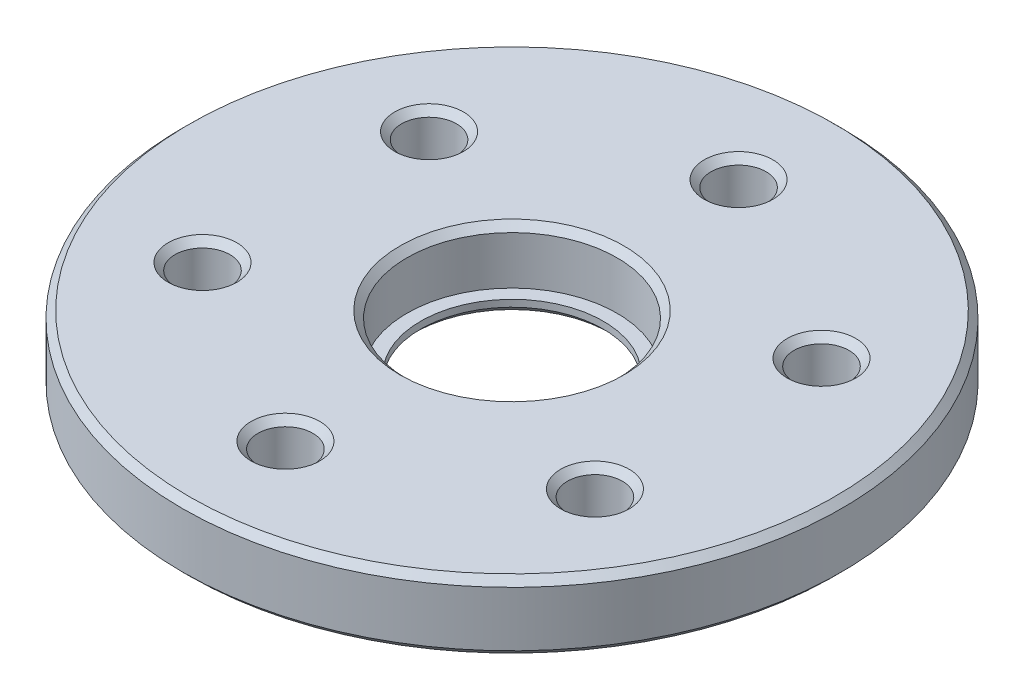
SolidWorks part; units mm, degrees
ref_plane "Front Plane" through (0, 0, 0) normal (0, 0, 1) x (1, 0, 0)
ref_plane "Top Plane" through (0, 0, 0) normal (0, 1, 0) x (1, 0, 0)
ref_plane "Right Plane" through (0, 0, 0) normal (1, 0, 0) x (0, 0, -1)
sketch "Sketch1" plane through (0, 0, 0) normal (0, 1, 0) x (1, 0, 0)
  circle A0 centre (0, 0) radius 24
  circle A1 centre (0, 0) radius 7.65
  dimension "D1" = 48
  dimension "D2" = 15.3
extrude "Boss-Extrude1" add sketch "Sketch1" along normal blind 4
sketch "Sketch2" plane through (0, 4, 0) normal (0, 1, 0) x (1, 0, 0)
  circle A0 centre (0, 16.5) radius 2
  dimension "D1" = 16.5
  dimension "D2" = 4
extrude "Cut-Extrude1" cut sketch "Sketch2" against normal through all
pattern_circular "CirPattern2" count 6 over 360 about axis through (0, 0, 0) along (0, 1, 0) of "Cut-Extrude1"
sketch "Sketch3" plane through (0, 0, 0) normal (0, 1, 0) x (1, 0, 0)
  circle A0 centre (-14.2894, -8.25) radius 2 construction
  circle A1 centre (0, -16.5) radius 2 construction
  circle A2 centre (14.2894, -8.25) radius 2 construction
  circle A3 centre (14.2894, 8.25) radius 2 construction
  circle A4 centre (0, 0) radius 24
  circle A5 centre (0, 16.5) radius 2 construction
  circle A6 centre (-14.2894, 8.25) radius 2 construction
  circle A7 centre (0, 0) radius 6.65
  circle A8 centre (-14.2894, -8.25) radius 2
  circle A9 centre (0, -16.5) radius 2
  circle A10 centre (14.2894, -8.25) radius 2
  circle A11 centre (14.2894, 8.25) radius 2
  circle A13 centre (0, 16.5) radius 2
  circle A14 centre (-14.2894, 8.25) radius 2
  circle A19 centre (0, 0) radius 24 construction
  circle A20 centre (0, 0) radius 7.65 construction
  dimension "D1" = 0
  dimension "D2" = 1
extrude "Boss-Extrude2" add sketch "Sketch3" against normal blind 1
chamfer "Chamfer1" distance 0.5 angle 45 16 edges at (0, 4, 7.65) (0, 4, 24) (0, 4, -14.5) (-12.5574, 4, -7.25) (-12.5574, 4, 7.25) (0, 4, 14.5) (12.5574, 4, 7.25) (12.5574, 4, -7.25) (0, -1, 24) (-14.2894, -1, 10.25) (0, -1, 6.65) (0, -1, 18.5) (14.2894, -1, 10.25) (14.2894, -1, -6.25) (0, -1, -14.5) (-14.2894, -1, -6.25)
